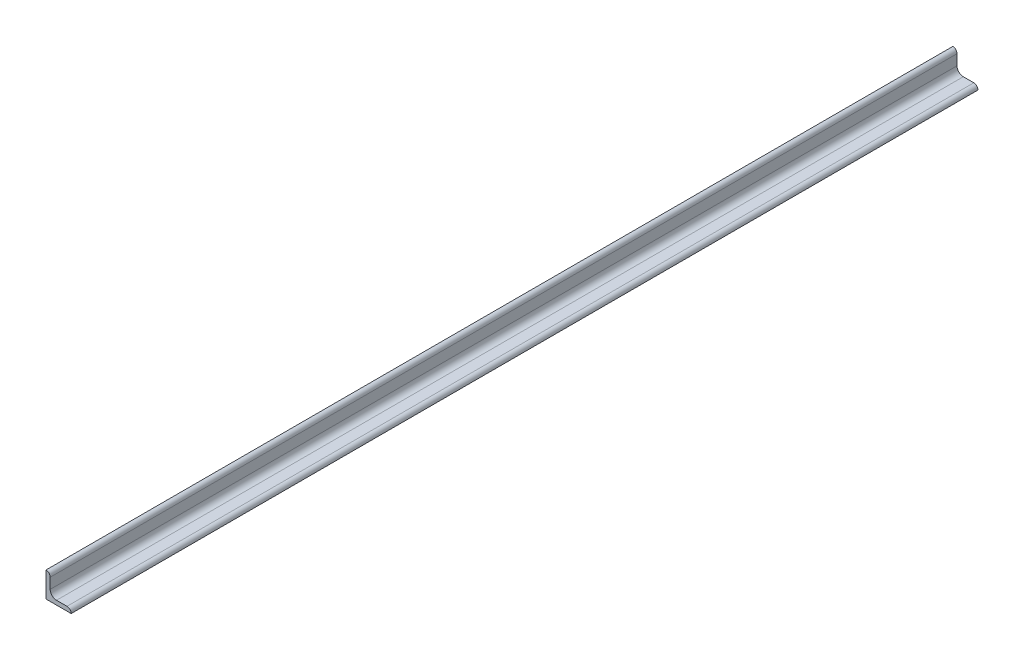
SolidWorks part; units mm, degrees
ref_plane "Plane1" through (0, 0, 0) normal (0, 0, 1) x (1, 0, 0)
ref_plane "Plane2" through (0, 0, 0) normal (0, 1, 0) x (1, 0, 0)
ref_plane "Plane3" through (0, 0, 0) normal (1, 0, 0) x (0, 0, -1)
sketch "Sketch1" plane through (0, 0, 0) normal (0, 0, 1) x (1, 0, 0)
  line L0 (0, 0) -> (0, 19.05)
  line L1 (0, 19.05) -> (0.0051, 19.05)
  line L2 (3.175, 15.8801) -> (3.175, 7.9375)
  line L3 (7.9375, 3.175) -> (15.8801, 3.175)
  line L4 (19.05, 0.0051) -> (19.05, 0)
  line L5 (19.05, 0) -> (0, 0)
  arc A0 (19.05, 0.0051) -> (15.8801, 3.175) centre (15.8801, 0.0051) ccw
  arc A1 (0.0051, 19.05) -> (3.175, 15.8801) centre (0.0051, 15.8801) cw
  arc A2 (7.9375, 3.175) -> (3.175, 7.9375) centre (7.9375, 7.9375) cw
  circle A3 centre (0, 0) radius 3.175 construction
  dimension "D2" = 0.0051
  dimension "Radius_1" = 4.7625
  dimension "Radius_2" = 3.175
  dimension "D1" = 3.175
  dimension "V_leg" = 19.05
  dimension "H_leg" = 19.05
  dimension "Thickness" = 3.175
  dimension "Flat_wid" = 0.0051
extrude "BaseSteelAngle" add sketch "Sketch1" along normal mid plane 685.8
equation "\"Flat_wid@Sketch1\" = ((sgn(\"Thickness@Sketch1\" - \"Radius_2@Sketch1\") +1)*(\"Thickness@Sketch1\" - \"Radius_2@Sketch1\"))/2 +0.0002"
equation "\"D1@Sketch1\" = \"Thickness@Sketch1\""
equation "\"D2@Sketch1\" = \"Flat_wid@Sketch1\""
